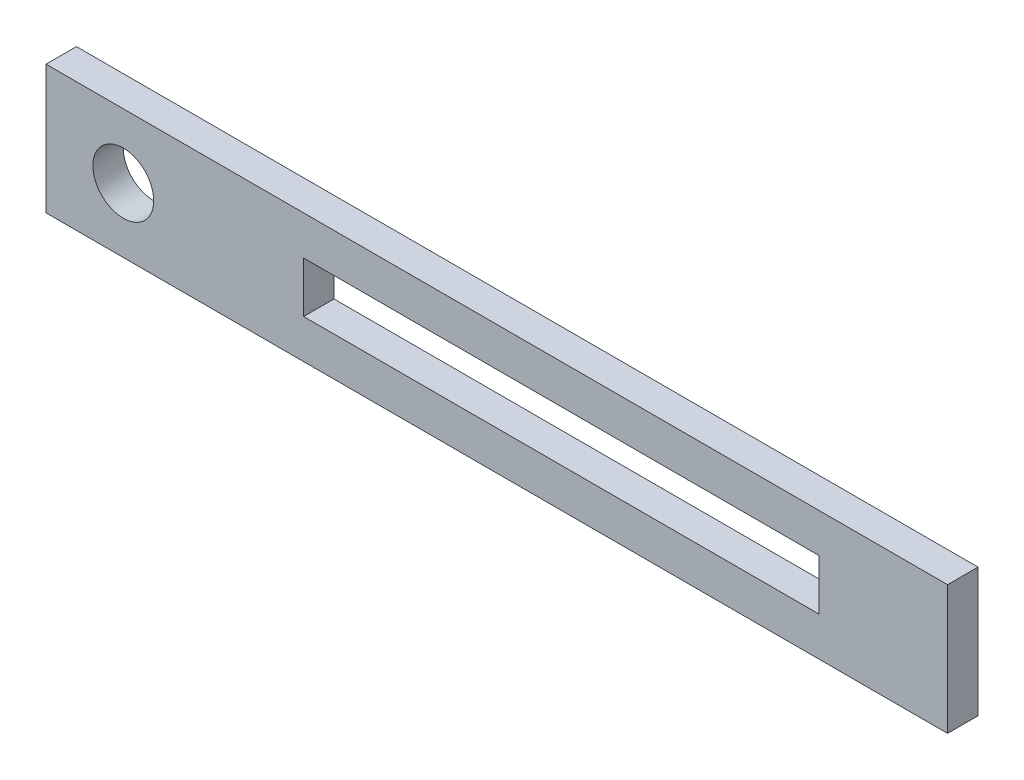
SolidWorks part; units mm, degrees
ref_plane "Front Plane" through (0, 0, 0) normal (0, 0, 1) x (1, 0, 0)
ref_plane "Top Plane" through (0, 0, 0) normal (0, 1, 0) x (1, 0, 0)
ref_plane "Right Plane" through (0, 0, 0) normal (1, 0, 0) x (0, 0, -1)
sketch "Sketch1" plane through (0, 0, 0) normal (0, 0, 1) x (1, 0, 0)
  line L0 (-7.62, 0) -> (81.28, 0) construction
  line L1 (-7.62, 6.35) -> (81.28, 6.35)
  line L2 (-7.62, 6.35) -> (-7.62, -6.35)
  line L3 (-7.62, -6.35) -> (81.28, -6.35)
  line L4 (81.28, 6.35) -> (81.28, -6.35)
  line L6 (17.78, 2.5) -> (68.58, 2.5)
  line L7 (17.78, 2.5) -> (17.78, -2.5)
  line L8 (17.78, -2.5) -> (68.58, -2.5)
  line L9 (68.58, 2.5) -> (68.58, -2.5)
  line L10 (17.78, 2.5) -> (68.58, -2.5) construction
  line L11 (17.78, -2.5) -> (68.58, 2.5) construction
  circle A0 centre (0, 0) radius 3
  point P9 (43.18, 0)
  dimension "D1" = 6
  dimension "D2" = 12.7
  dimension "D3" = 7.62
  dimension "D4" = 88.9
  dimension "D5" = 5
  dimension "D6" = 38.1
  dimension "D7" = 50.8
extrude "Boss-Extrude1" add sketch "Sketch1" along normal mid plane 3
